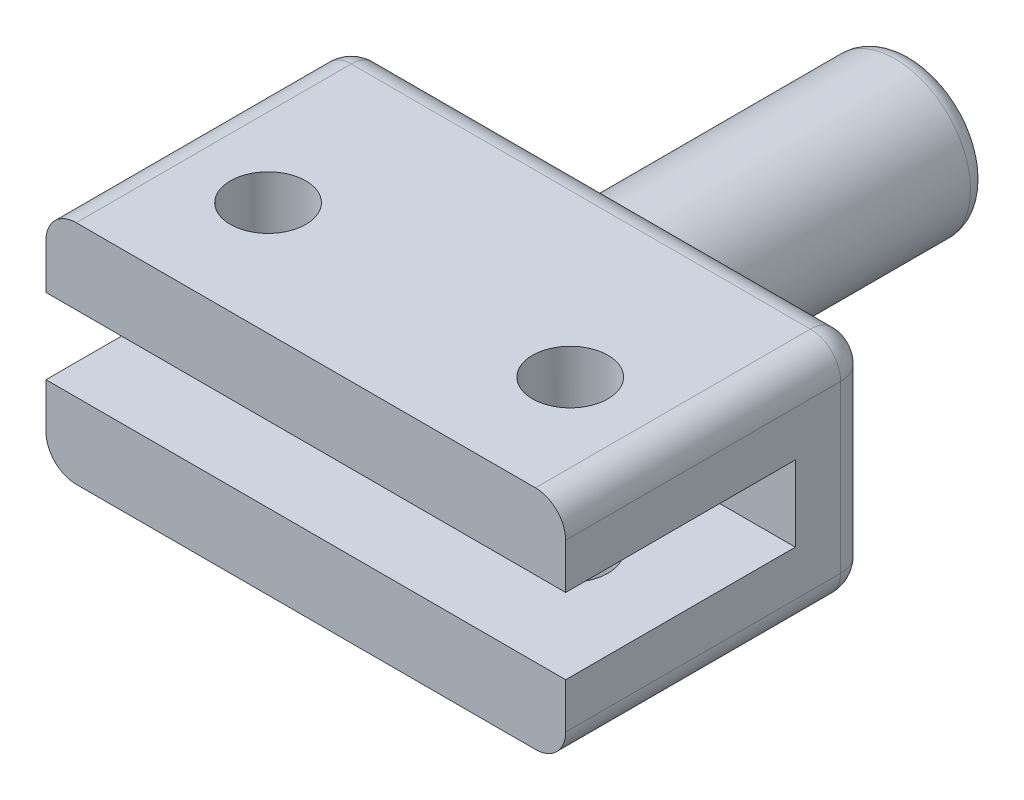
SolidWorks part; units mm, degrees
material "ABS"
ref_plane "Front Plane" through (0, 0, 0) normal (0, 0, 1) x (1, 0, 0)
ref_plane "Top Plane" through (0, 0, 0) normal (0, 1, 0) x (1, 0, 0)
ref_plane "Right Plane" through (0, 0, 0) normal (1, 0, 0) x (0, 0, -1)
sketch "Sketch1" plane through (0, 0, 0) normal (0, 1, 0) x (1, 0, 0)
  line L1 (0, 12.7) -> (3.175, 12.7)
  line L2 (0, 12.7) -> (0, 0)
  line L3 (0, 0) -> (3.175, 0)
  line L4 (3.175, 12.7) -> (3.175, 0)
  dimension "D1" = 12.7
  dimension "D2" = 3.175
revolve "Revolve1" add sketch "Sketch1" angle 360 about L2
sketch "Sketch2" plane through (0, 0, 0) normal (0, 0, 1) x (1, 0, 0)
  line L0 (0, 4.7625) -> (0, -4.7625) construction
  line L1 (-10.922, 4.7625) -> (10.922, 4.7625)
  line L2 (-10.922, 4.7625) -> (-10.922, -4.7625)
  line L3 (-10.922, -4.7625) -> (10.922, -4.7625)
  line L4 (10.922, 4.7625) -> (10.922, -4.7625)
  line L5 (-10.922, 0) -> (10.922, 0) construction
  dimension "D1" = 9.525
  dimension "D2" = 21.844
extrude "Boss-Extrude1" add sketch "Sketch2" along normal blind 12.827
fillet "Fillet4" radius 1.27 8 edges at (-10.922, -4.7625, 6.4135) (10.922, -4.7625, 6.4135) (0, -4.7625, 0) (-10.922, 4.7625, 6.4135) (10.922, 4.7625, 6.4135) (10.922, 0, 0) (-10.922, 0, 0) (0, 4.7625, 0)
sketch "Sketch3" plane through (-10.922, 0, 0) normal (-1, 0, 0) x (0, 0, 1)
  line L0 (12.827, 3.4925) -> (12.827, -3.4925) construction
  line L1 (3.175, 1.5875) -> (12.827, 1.5875)
  line L2 (3.175, 1.5875) -> (3.175, -1.5875)
  line L3 (3.175, -1.5875) -> (12.827, -1.5875)
  line L4 (12.827, 1.5875) -> (12.827, -1.5875)
  point P4 (12.827, 0)
  point P5 (12.827, 0)
  dimension "D1" = 3.175
  dimension "D2" = 9.652
extrude "Cut-Extrude1" cut sketch "Sketch3" against normal through all
sketch "Sketch4" plane through (0, 4.7625, 0) normal (0, 1, 0) x (1, 0, 0)
  line L0 (0, -1.27) -> (0, -12.827) construction
  line L1 (9.652, -1.27) -> (-9.652, -1.27) construction
  line L2 (9.652, -12.827) -> (-9.652, -12.827) construction
  circle A0 centre (-6.35, -8.0645) radius 1.5875
  circle A1 centre (6.35, -8.0645) radius 1.5875
  dimension "D2" = 3.175
  dimension "D1" = 4.7625
  dimension "D3" = 6.35
extrude "Cut-Extrude2" cut sketch "Sketch4" against normal through all
fillet "Fillet5" radius 0.762 2 edges at (3.175, 0, 0) (-3.175, 0, -12.7)
